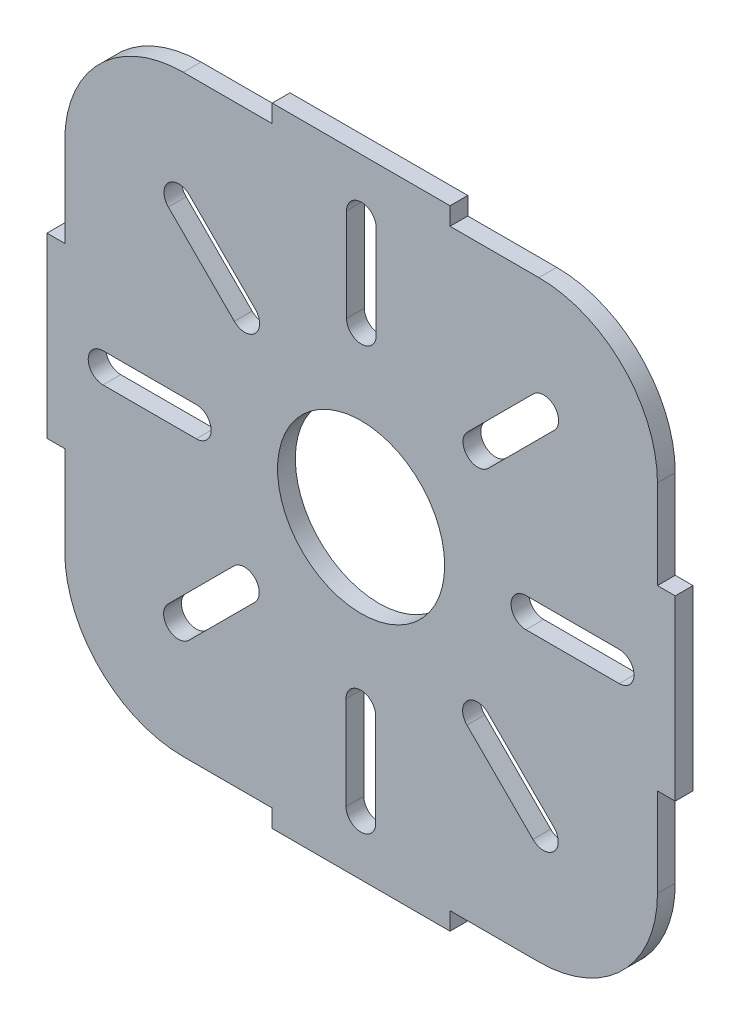
SolidWorks part; units mm, degrees
ref_plane "Plan de face" through (0, 0, 0) normal (0, 0, 1) x (1, 0, 0)
ref_plane "Plan de dessus" through (0, 0, 0) normal (0, 1, 0) x (1, 0, 0)
ref_plane "Plan de droite" through (0, 0, 0) normal (1, 0, 0) x (0, 0, -1)
sketch "Esquisse1" plane through (0, 0, 0) normal (0, 0, 1) x (1, 0, 0)
  line L0 (0, 0) -> (0, 35)
  line L1 (0, 100) -> (35, 100)
  line L2 (100, 100) -> (100, 65)
  line L3 (100, 0) -> (65, 0)
  line L4 (-3, 35) -> (-3, 65)
  line L5 (-3, 65) -> (0, 65)
  line L6 (-3, 35) -> (0, 35)
  line L7 (35, 103) -> (65, 103)
  line L8 (65, 103) -> (65, 100)
  line L9 (35, 103) -> (35, 100)
  line L10 (103, 65) -> (103, 35)
  line L11 (103, 35) -> (100, 35)
  line L12 (103, 65) -> (100, 65)
  line L13 (65, -3) -> (35, -3)
  line L14 (35, -3) -> (35, 0)
  line L15 (65, -3) -> (65, 0)
  line L16 (65, 100) -> (100, 100)
  line L17 (100, 35) -> (100, 0)
  line L18 (35, 0) -> (0, 0)
  line L19 (0, 65) -> (0, 100)
  point P8 (-3, 50)
  point P25 (50, 50)
  dimension "D1" = 100
  dimension "D3" = 3
  dimension "D4" = 30
  dimension "D5" = 4
extrude "Boss.-Extru.1" add sketch "Esquisse1" along normal blind 3
sketch "Esquisse3" plane through (0, 0, 3) normal (0, 0, 1) x (1, 0, 0)
  line L0 (100, 100) -> (0, 0) construction
  line L1 (0, 100) -> (100, 0) construction
sketch "Esquisse2" plane through (0, 0, 3) normal (0, 0, 1) x (1, 0, 0)
  line L0 (100, 100) -> (0, 0) construction
  circle A0 centre (50, 50) radius 14.1
  dimension "D1" = 28.2
extrude "Enlèv. mat.-Extru.1" cut sketch "Esquisse2" against normal up to surface (3 mm away) up to face at (50, 50, 0)
fillet "Congé1" radius 20 4 edges at (0, 0, 1.5) (100, 0, 1.5) (100, 100, 1.5) (0, 100, 1.5)
sketch "Esquisse4" plane through (0, 0, 3) normal (0, 0, 1) x (1, 0, 0)
  line L0 (50.0449, 93.5427) -> (50.0449, 77.8009) construction
  line L1 (52.5449, 93.5427) -> (52.5449, 77.8009)
  line L2 (47.5449, 93.5427) -> (47.5449, 77.8009)
  arc A0 (52.5449, 93.5427) -> (47.5449, 93.5427) centre (50.0449, 93.5427) ccw
  arc A1 (47.5449, 77.8009) -> (52.5449, 77.8009) centre (50.0449, 77.8009) ccw
  point P2 (50.0449, 85.6718)
  dimension "D1" = 5
extrude "Enlèv. mat.-Extru.2" cut sketch "Esquisse4" against normal up to next (3 mm away)
pattern_circular "Répétition circulaire1" count 8 over 360 about axis through (50, 50, 0) along (0, 0, 1) of "Enlèv. mat.-Extru.2"
